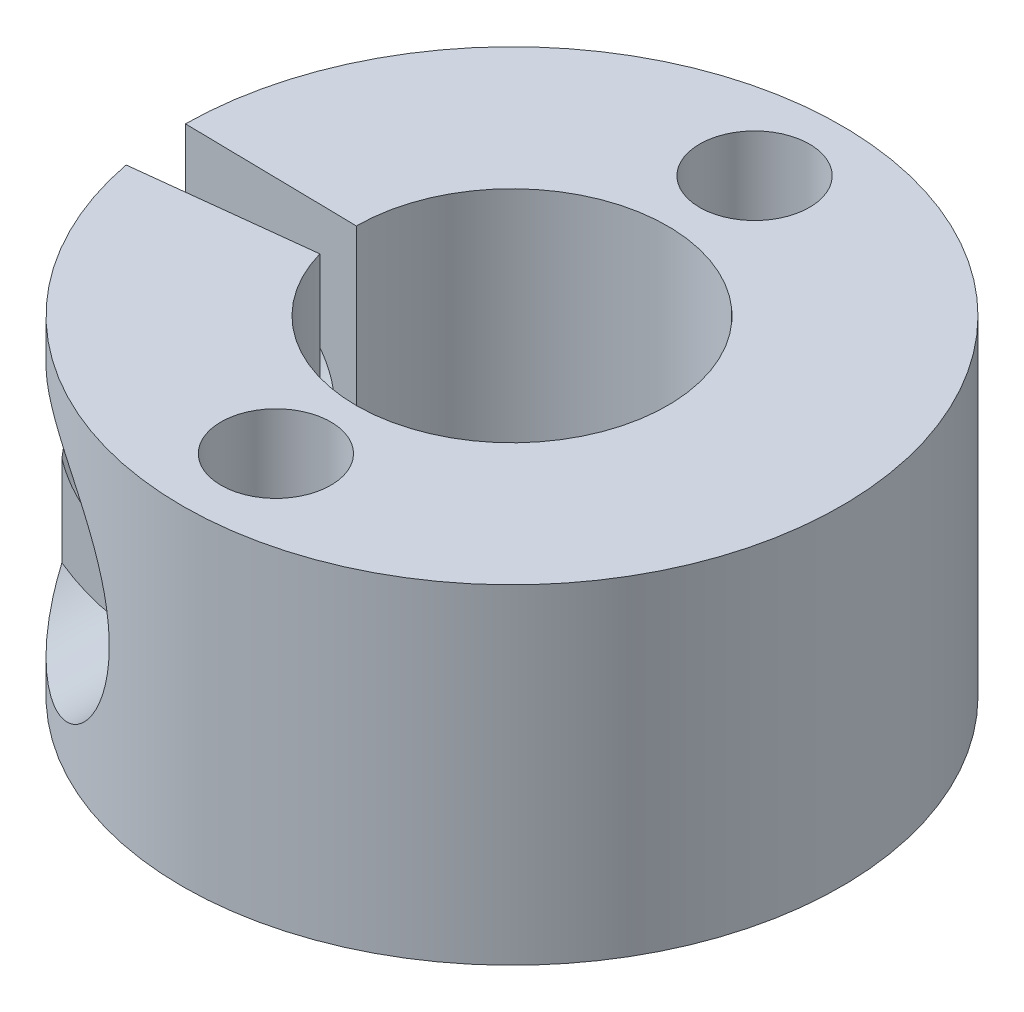
SolidWorks part; units mm, degrees
ref_plane "Front Plane" through (0, 0, 0) normal (0, 0, 1) x (1, 0, 0)
ref_plane "Top Plane" through (0, 0, 0) normal (0, 1, 0) x (1, 0, 0)
ref_plane "Right Plane" through (0, 0, 0) normal (1, 0, 0) x (0, 0, -1)
sketch "Sketch1" plane through (0, 0, 0) normal (0, 1, 0) x (1, 0, 0)
  line L0 (-8.9996, 0.0812) -> (-4.25, 0)
  line L5 (-4.0887, -1.1597) -> (-8.8375, -1.7026)
  circle A0 centre (0, 0) radius 9
  circle A1 centre (0, 0) radius 4.25
  dimension "D1" = 18
  dimension "D2" = 8.5
extrude "Boss-Extrude1" add sketch "Sketch1" along normal blind 9 contours A1 L5 A0 L0
sketch "Sketch2" plane through (0.0781, 0, 0.6833) normal (-0.1136, 0, -0.9935) x (-0.9935, 0, 0.1136)
  line L0 (4.194, 0) -> (8.9737, 9) construction
  line L1 (8.9737, 9) -> (4.194, 9) construction
  line L2 (4.194, 9) -> (8.9737, 0) construction
  circle A0 centre (6.5838, 4.5) radius 1.75
  dimension "D1" = 3.5
extrude "Cut-Extrude1" cut sketch "Sketch2" against normal through all both and the other way through all
ref_plane "Plane1" through (0, 0, 10) normal (0, 0, 1) x (1, 0, 0)
sketch "Sketch3" plane through (0, 0, 10) normal (0, 0, 1) x (1, 0, 0)
  circle A0 centre (-5.7984, 4.3849) radius 3.5
  dimension "D1" = 7
extrude "Cut-Extrude2" cut sketch "Sketch3" against normal blind 5.5
ref_plane "Plane2" through (0, 0, -10) normal (0, 0, 1) x (1, 0, 0)
sketch "Sketch4" plane through (0, 0, -10) normal (0, 0, 1) x (1, 0, 0)
  circle A0 centre (-7.2636, 4.4806) radius 3.5
  dimension "D1" = 7
extrude "Cut-Extrude3" cut sketch "Sketch4" along normal blind 7
sketch "Sketch5" plane through (0, 9, 0) normal (0, 1, 0) x (1, 0, 0)
  line L0 (0, -9) -> (0, -4.25) construction
  line L2 (0, 4.25) -> (0, 9) construction
  arc A1 (-8.8375, -1.7026) -> (-8.9996, 0.0812) centre (0, 0) ccw construction
  arc A2 (-4.0887, -1.1597) -> (-4.25, 0) centre (0, 0) ccw construction
  circle A3 centre (0.0355, -6.4842) radius 1.5
  circle A4 centre (0, 6.625) radius 1.5
  dimension "D1" = 3
extrude "Cut-Extrude4" cut sketch "Sketch5" against normal through all
